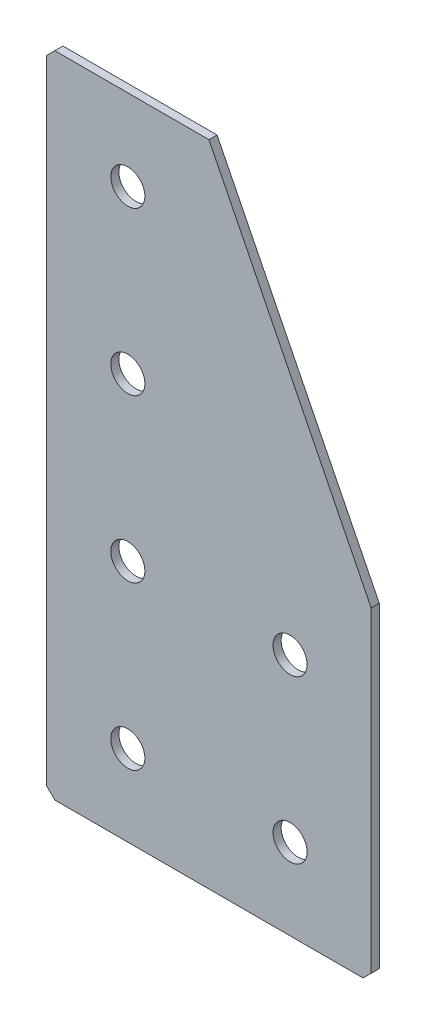
SolidWorks part; units mm, degrees
material "Простая углеродистая сталь"
ref_plane "Спереди(Плоскость XY)" through (0, 0, 0) normal (0, 0, 1) x (1, 0, 0)
ref_plane "Сверху(Плоскость XZ)" through (0, 0, 0) normal (0, 1, 0) x (1, 0, 0)
ref_plane "Справа(Плоскость ZY)" through (0, 0, 0) normal (1, 0, 0) x (0, 0, -1)
sketch "Эскиз1" plane through (0, 0, 0) normal (0, 0, -1) x (1, 0, 0)
  line L0 (0, 0) -> (0, 160)
  line L1 (0, 160) -> (80, 160)
  line L2 (80, 160) -> (80, 80)
  line L3 (80, 80) -> (40, 80) construction
  line L4 (40, 80) -> (40, 0) construction
  line L5 (40, 0) -> (0, 0)
  line L6 (80, 80) -> (40, 0)
  dimension "D1" = 160
  dimension "D2" = 80
  dimension "D3" = 40
  dimension "D4" = 40
extrude "Бобышка-Вытянуть1" add sketch "Эскиз1" along normal blind 2
hole_wizard "Отверстие с зазором M81" positions "Эскиз2" profile "Эскиз3" hole size "M8" standard "DIN" end condition up to next
sketch "Эскиз2" plane through (0, 0, -2) normal (0, 0, -1) x (1, 0, 0)
  line L0 (20, 0) -> (20, 160) construction
  line L1 (0, 0) -> (40, 0) construction
  line L2 (80, 160) -> (0, 160) construction
  point P0 (20, 140)
  point P2 (20, 100)
  point P4 (20, 60)
  point P6 (20, 20)
  point P27 (60, 140)
  point P29 (60, 100)
  dimension "D1" = 40
  dimension "D2" = 40
  dimension "D3" = 40
  dimension "D4" = 20
  dimension "D5" = 40
sketch "Эскиз3" plane through (20, -140, -2) normal (1, 0, 0) x (0, 1, 0)
  line L0 (0, 0) -> (0, 2)
  line L1 (0, 2) -> (4.2, 2)
  line L2 (4.2, 2) -> (4.2, 0)
  line L5 (4.2, 0) -> (0, 0)
  line L11 (0, -6.35) -> (0, 107.95) construction
  dimension "Диаметр сквозного отверстия" = 8.4
  dimension "Глубина сквозного отверстия" = 2
chamfer "Фаска1" distance 2 angle 45 3 edges at (0, 0, -1) (80, -160, -1) (0, -160, -1)
